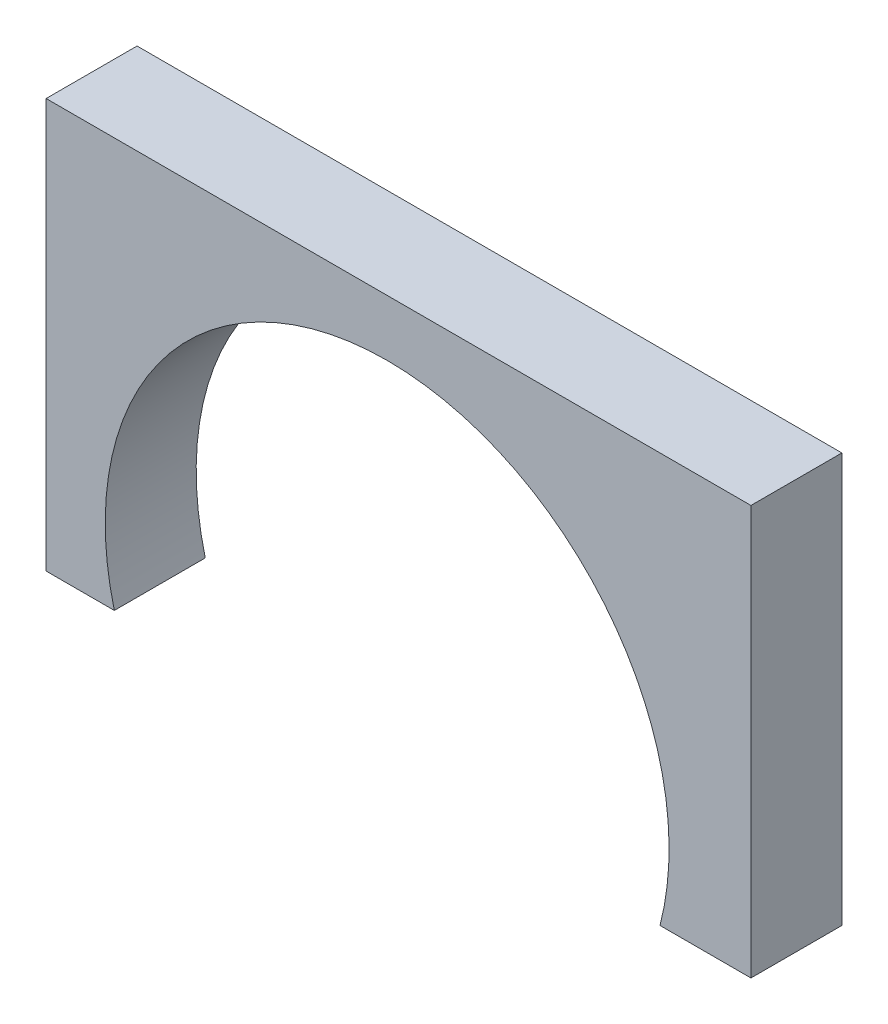
SolidWorks part; units mm, degrees
ref_plane "Front Plane" through (0, 0, 0) normal (0, 0, 1) x (1, 0, 0)
ref_plane "Top Plane" through (0, 0, 0) normal (0, 1, 0) x (1, 0, 0)
ref_plane "Right Plane" through (0, 0, 0) normal (1, 0, 0) x (0, 0, -1)
sketch "Sketch1" plane through (0, 0, 0) normal (0, 0, 1) x (1, 0, 0)
  line L6 (0, 74.3795) -> (0, -15.6205) construction
  line L7 (-75, 74.3795) -> (-75, -15.6205)
  line L10 (80, 74.3795) -> (80, -15.6205)
  line L12 (-60, -15.6205) -> (60, -15.6205) construction
  line L13 (-60, -15.6205) -> (-75, -15.6205)
  line L14 (60, -15.6205) -> (80, -15.6205)
  line L15 (-75, 74.3795) -> (80, 74.3795)
  arc A2 (60, -15.6205) -> (-60, -15.6205) centre (0, 0) ccw
  dimension "D1" = 62
  dimension "D3" = 75
  dimension "D4" = 120
  dimension "D2" = 80
  dimension "D5" = 90
extrude "Boss-Extrude1" add sketch "Sketch1" along normal blind 20
